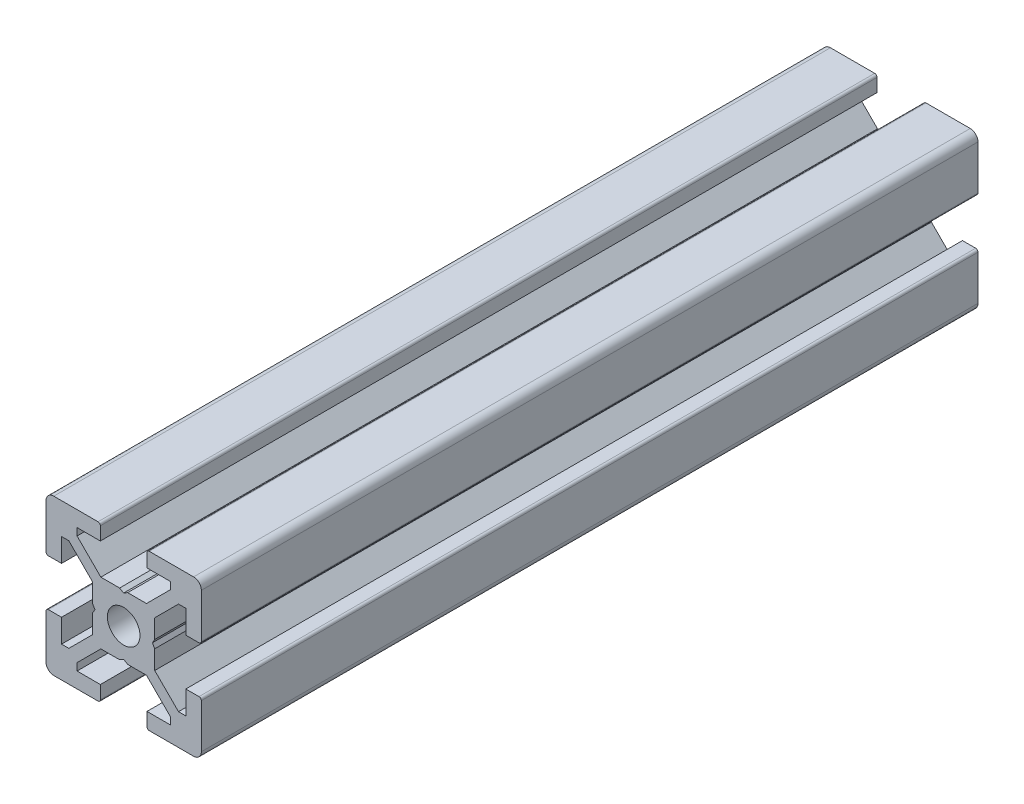
SolidWorks part; units mm, degrees
material "6063-T5"
ref_plane "Front Plane" through (0, 0, 0) normal (0, 0, 1) x (1, 0, 0)
ref_plane "Top Plane" through (0, 0, 0) normal (0, 1, 0) x (1, 0, 0)
ref_plane "Right Plane" through (0, 0, 0) normal (1, 0, 0) x (0, 0, -1)
ref_plane "Plane1" through (0, 0, 0) normal (0, 0, 1) x (1, 0, 0)
sketch "Sketch1" plane through (0, 0, 0) normal (0, 0, 1) x (1, 0, 0)
  line L0 (-10, 9) -> (-10, 3.3)
  line L1 (-9.7, 3) -> (-8, 3)
  line L2 (-8, 3) -> (-8, 6)
  line L3 (-8, 6) -> (-7.0607, 6)
  line L4 (-7.0607, 6) -> (-4, 2.9393)
  line L5 (-4, 2.9393) -> (-4, 0.5196)
  line L6 (-4, 0.5196) -> (-3.7, 0)
  line L7 (-3.7, 0) -> (-4, -0.5196)
  line L8 (-4, -0.5196) -> (-4, -2.9393)
  line L9 (-4, -2.9393) -> (-7.0607, -6)
  line L10 (-7.0607, -6) -> (-8, -6)
  line L11 (-8, -6) -> (-8, -3)
  line L12 (-8, -3) -> (-9.7, -3)
  line L13 (-10, -3.3) -> (-10, -9)
  line L14 (-9, -10) -> (-3.3, -10)
  line L15 (-3, -9.7) -> (-3, -8)
  line L16 (-3, -8) -> (-6, -8)
  line L17 (-6, -8) -> (-6, -7.0607)
  line L18 (-6, -7.0607) -> (-2.9393, -4)
  line L19 (-2.9393, -4) -> (-0.5196, -4)
  line L20 (-0.5196, -4) -> (0, -3.7)
  line L21 (0, -3.7) -> (0.5196, -4)
  line L22 (0.5196, -4) -> (2.9393, -4)
  line L23 (2.9393, -4) -> (6, -7.0607)
  line L24 (6, -7.0607) -> (6, -8)
  line L25 (6, -8) -> (3, -8)
  line L26 (3, -8) -> (3, -9.7)
  line L27 (3.3, -10) -> (9, -10)
  line L28 (10, -9) -> (10, -3.3)
  line L29 (9.7, -3) -> (8, -3)
  line L30 (8, -3) -> (8, -6)
  line L31 (8, -6) -> (7.0606, -6)
  line L32 (7.0606, -6) -> (4, -2.9393)
  line L33 (4, -2.9393) -> (4, -0.5196)
  line L34 (4, -0.5196) -> (3.7, 0)
  line L35 (3.7, 0) -> (4, 0.5196)
  line L36 (4, 0.5196) -> (4, 2.9393)
  line L37 (4, 2.9393) -> (7.0607, 6)
  line L38 (7.0607, 6) -> (8, 6)
  line L39 (8, 6) -> (8, 3)
  line L40 (8, 3) -> (9.7, 3)
  line L41 (10, 3.3) -> (10, 9)
  line L42 (9, 10) -> (3.3, 10)
  line L43 (3, 9.7) -> (3, 8)
  line L44 (3, 8) -> (6, 8)
  line L45 (6, 8) -> (6, 7.0607)
  line L46 (6, 7.0607) -> (2.9393, 4)
  line L47 (2.9393, 4) -> (0.5196, 4)
  line L48 (0.5196, 4) -> (0, 3.7)
  line L49 (0, 3.7) -> (-0.5196, 4)
  line L50 (-0.5196, 4) -> (-2.9394, 4)
  line L51 (-2.9394, 4) -> (-6, 7.0606)
  line L52 (-6, 7.0606) -> (-6, 8)
  line L53 (-6, 8) -> (-3, 8)
  line L54 (-3, 8) -> (-3, 9.7)
  line L55 (-3.3, 10) -> (-9, 10)
  arc A0 (-10, 3.3) -> (-9.7, 3) centre (-9.7, 3.3) ccw
  arc A1 (-9.7, -3) -> (-10, -3.3) centre (-9.7, -3.3) ccw
  arc A2 (-10, -9) -> (-9, -10) centre (-9, -9) ccw
  arc A3 (-3.3, -10) -> (-3, -9.7) centre (-3.3, -9.7) ccw
  arc A4 (3, -9.7) -> (3.3, -10) centre (3.3, -9.7) ccw
  arc A5 (9, -10) -> (10, -9) centre (9, -9) ccw
  arc A6 (10, -3.3) -> (9.7, -3) centre (9.7, -3.3) ccw
  arc A7 (9.7, 3) -> (10, 3.3) centre (9.7, 3.3) ccw
  arc A8 (10, 9) -> (9, 10) centre (9, 9) ccw
  arc A9 (3.3, 10) -> (3, 9.7) centre (3.3, 9.7) ccw
  arc A10 (-3, 9.7) -> (-3.3, 10) centre (-3.3, 9.7) ccw
  arc A11 (-9, 10) -> (-10, 9) centre (-9, 9) ccw
extrude "Boss-Extrude1" add sketch "Sketch1" against normal blind 100
ref_plane "Plane2" through (0, 0, 0) normal (1, 0, 0) x (0, 0, -1)
sketch "Sketch2" plane through (0, 0, 0) normal (1, 0, 0) x (0, 0, -1)
  line L0 (0, 0) -> (0, 2.1)
  line L1 (0, 2.1) -> (100, 2.1)
  line L2 (100, 2.1) -> (100, 0)
  line L3 (100, 0) -> (0, 0)
  line L4 (100, 0) -> (0, 0) construction
  dimension "D1" = 2.1
  dimension "D2" = 100
revolve "Cut-Revolve1" cut sketch "Sketch2" angle 360 about L4
ref_plane "Plane3" through (0, 0, -50) normal (0, 0, 1) x (1, 0, 0)
sketch "Sketch4" plane through (4, 0, 0) normal (1, 0, 0) x (0, 0, -1)
  line L0 (100, 0) -> (0, 0) construction
  line L1 (0, -2.9393) -> (0, -0.5196) construction
  line L2 (50, 2.9393) -> (50, -2.9393) construction
  line L3 (100, 2.9393) -> (0, 2.9393) construction
  line L4 (100, -2.9393) -> (0, -2.9393) construction
  circle A0 centre (10, 0) radius 2.5
  dimension "D1" = 5
  dimension "D2" = 10
extrude "Cut-Extrude1" cut sketch "Sketch4" against normal up to surface (8 mm away) up to face at (-4, 1.7295, -50)
